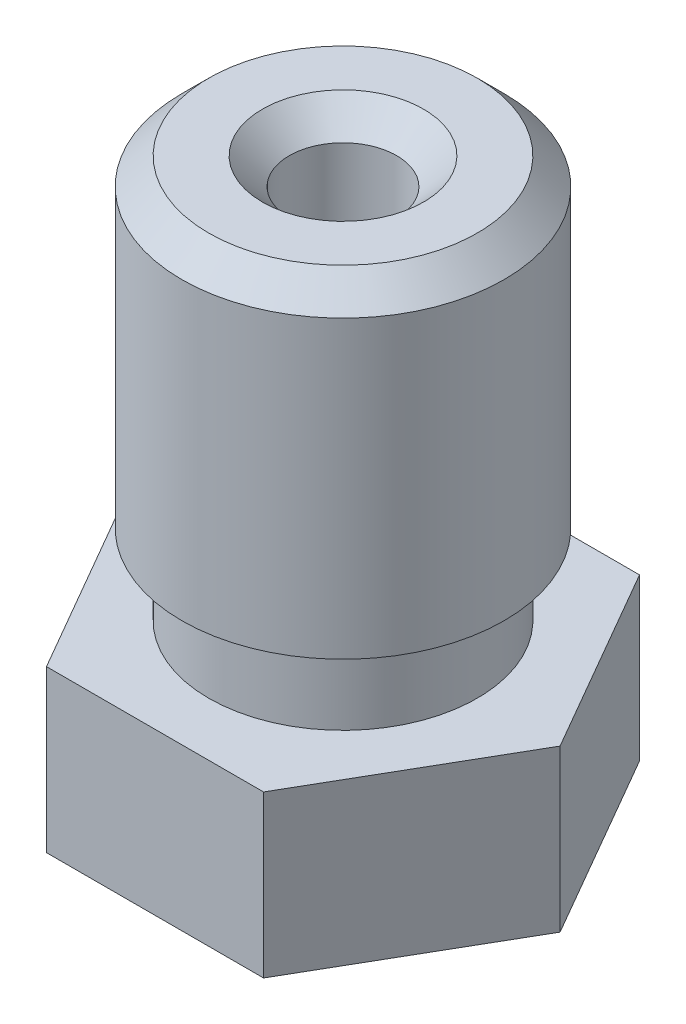
SolidWorks part; units mm, degrees
material "Brass"
ref_plane "Front Plane" through (0, 0, 0) normal (0, 0, 1) x (1, 0, 0)
ref_plane "Top Plane" through (0, 0, 0) normal (0, 1, 0) x (1, 0, 0)
ref_plane "Right Plane" through (0, 0, 0) normal (1, 0, 0) x (0, 0, -1)
ref_plane "Plane1" through (0, 0, 0) normal (0, -1, 0) x (1, 0, 0)
sketch "Sketch1" plane through (0, 0, 0) normal (0, -1, 0) x (1, 0, 0)
  line L0 (-2.0207, 3.5) -> (-4.0415, 0)
  line L1 (-4.0415, 0) -> (-2.0207, -3.5)
  line L2 (-2.0207, -3.5) -> (2.0207, -3.5)
  line L3 (2.0207, -3.5) -> (4.0415, 0)
  line L4 (4.0415, 0) -> (2.0207, 3.5)
  line L5 (2.0207, 3.5) -> (-2.0207, 3.5)
extrude "Boss-Extrude1" add sketch "Sketch1" against normal blind 3
ref_plane "Plane2" through (0, 0, 0) normal (0, 0, -1) x (-1, 0, 0)
sketch "Sketch2" plane through (0, 0, 0) normal (0, 0, -1) x (-1, 0, 0)
  line L0 (-2.5, 3) -> (0, 3)
  line L1 (0, 3) -> (0, 10.5)
  line L2 (0, 10.5) -> (-3, 10.5)
  line L3 (-3, 10.5) -> (-3, 4.5)
  line L4 (-3, 4.5) -> (-2.5, 4.5)
  line L5 (-2.5, 4.5) -> (-2.5, 3)
  line L6 (0, 3) -> (0, 10.5) construction
revolve "Revolve1" add sketch "Sketch2" angle 360 about L6
sketch "Sketch3" plane through (0, 0, 0) normal (0, 0, 1) x (1, 0, 0)
  line L0 (2.5, 0) -> (0, 0)
  line L1 (0, 0) -> (0, -2)
  line L2 (0, -2) -> (0.5, -2)
  line L3 (0.5, -2) -> (2.5, 0)
  line L4 (0, 0) -> (0, -2) construction
revolve "Revolve2" add sketch "Sketch3" angle 360 about L4
sketch "Sketch4" plane through (0, 0, 0) normal (0, 0, -1) x (-1, 0, 0)
  line L0 (-0.05, -2) -> (0, -2)
  line L1 (0, -2) -> (0, 10.5)
  line L2 (0, 10.5) -> (-1, 10.5)
  line L3 (-1, 10.5) -> (-1, 0)
  line L4 (-1, 0) -> (-0.75, -0.2273)
  line L5 (-0.75, -0.2273) -> (-0.75, -0.7)
  line L6 (-0.75, -0.7) -> (-0.05, -1.2)
  line L7 (-0.05, -1.2) -> (-0.05, -2)
  line L8 (0, -2) -> (0, 10.5) construction
  dimension "D1" = 1
  dimension "D2" = 0.05
  dimension "D3" = 0.75
  dimension "D4" = 0.5
  dimension "D5" = 0.8
  dimension "D6" = 0.2273
  dimension "D7" = 0.4727
revolve "Cut-Revolve1" cut sketch "Sketch4" angle 360 about L8
chamfer "Chamfer1" distance 0.5 angle 45 2 edges at (0, 10.5, 3) (0, 10.5, 1)
